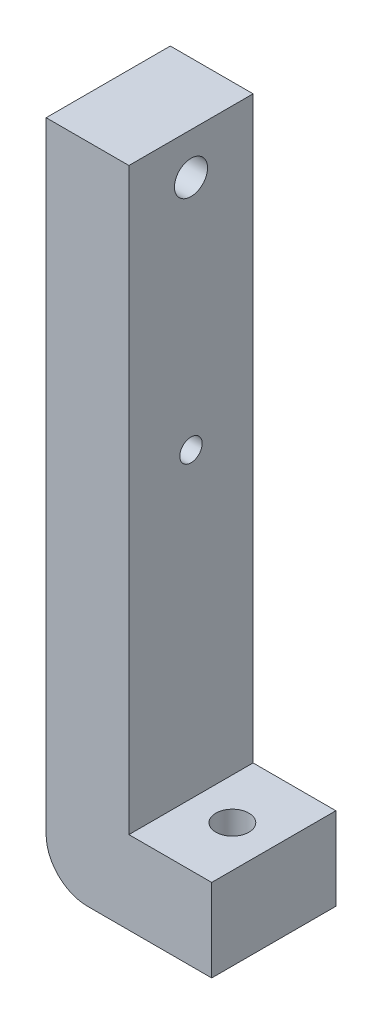
SolidWorks part; units mm, degrees
ref_plane "Front Plane" through (0, 0, 0) normal (0, 0, 1) x (1, 0, 0)
ref_plane "Top Plane" through (0, 0, 0) normal (0, 1, 0) x (1, 0, 0)
ref_plane "Right Plane" through (0, 0, 0) normal (1, 0, 0) x (0, 0, -1)
sketch "Sketch1" plane through (0, 0, 0) normal (0, 0, 1) x (1, 0, 0)
  line L0 (0, 20) -> (0, -10)
  line L1 (-10, -20) -> (10, -20)
  line L2 (-10, -20) -> (-10, 20)
  line L3 (-10, 20) -> (0, 20)
  line L4 (10, -20) -> (10, -10)
  line L5 (-10, -20) -> (0, 0) construction
  line L6 (-10, 20) -> (10, -20) construction
  line L7 (0, -10) -> (10, -10)
  point P0 (0, 0)
  dimension "D1" = 20
  dimension "D2" = 40
  dimension "D3" = 10
  dimension "D4" = 20
extrude "Boss-Extrude1" add sketch "Sketch1" along normal blind 15
fillet "Fillet1" radius 5 1 edges at (-10, -20, 7.5)
sketch "Sketch2" plane through (0, 20, 0) normal (0, 1, 0) x (1, 0, 0)
  line L4 (0, 0) -> (-10, 0)
  line L5 (-10, 0) -> (-10, -15)
  line L6 (-10, -15) -> (0, -15)
  line L7 (0, -15) -> (0, 0)
  line L8 (0, 0) -> (-10, 0)
  line L9 (-10, 0) -> (-10, -15)
  line L10 (-10, -15) -> (0, -15)
  line L11 (0, -15) -> (0, 0)
  dimension "D1" = 0
extrude "Boss-Extrude2" add sketch "Sketch2" along normal blind 40
sketch "Sketch3" plane through (0, -20, 0) normal (0, -1, 0) x (1, 0, 0)
  line L0 (5, 15) -> (5, 0) construction
  line L4 (-5, 15) -> (10, 15) construction
  line L5 (-5, 0) -> (10, 0) construction
  line L6 (10, 15) -> (10, 0) construction
  circle A0 centre (5, 7.5) radius 2
  dimension "D1" = 4
  dimension "D2" = 5
extrude "Cut-Extrude1" cut sketch "Sketch3" against normal through all
sketch "Sketch4" plane through (-10, 0, 0) normal (-1, 0, 0) x (0, 0, 1)
  circle A0 centre (7.5, 55) radius 2
extrude "Cut-Extrude2" cut sketch "Sketch4" against normal through all
sketch "Sketch5" plane through (-10, 0, 0) normal (-1, 0, 0) x (0, 0, 1)
  line L0 (7.5, 60) -> (7.5, 8.3297) construction
  line L1 (0, 60) -> (15, 60) construction
  line L2 (7.5, 26.5) -> (0, 26.5) construction
  line L3 (0, 60) -> (0, -15) construction
  circle A0 centre (7.5, 26.5) radius 1.35
  dimension "D1" = 2.7
extrude "Cut-Extrude3" cut sketch "Sketch5" against normal through all
